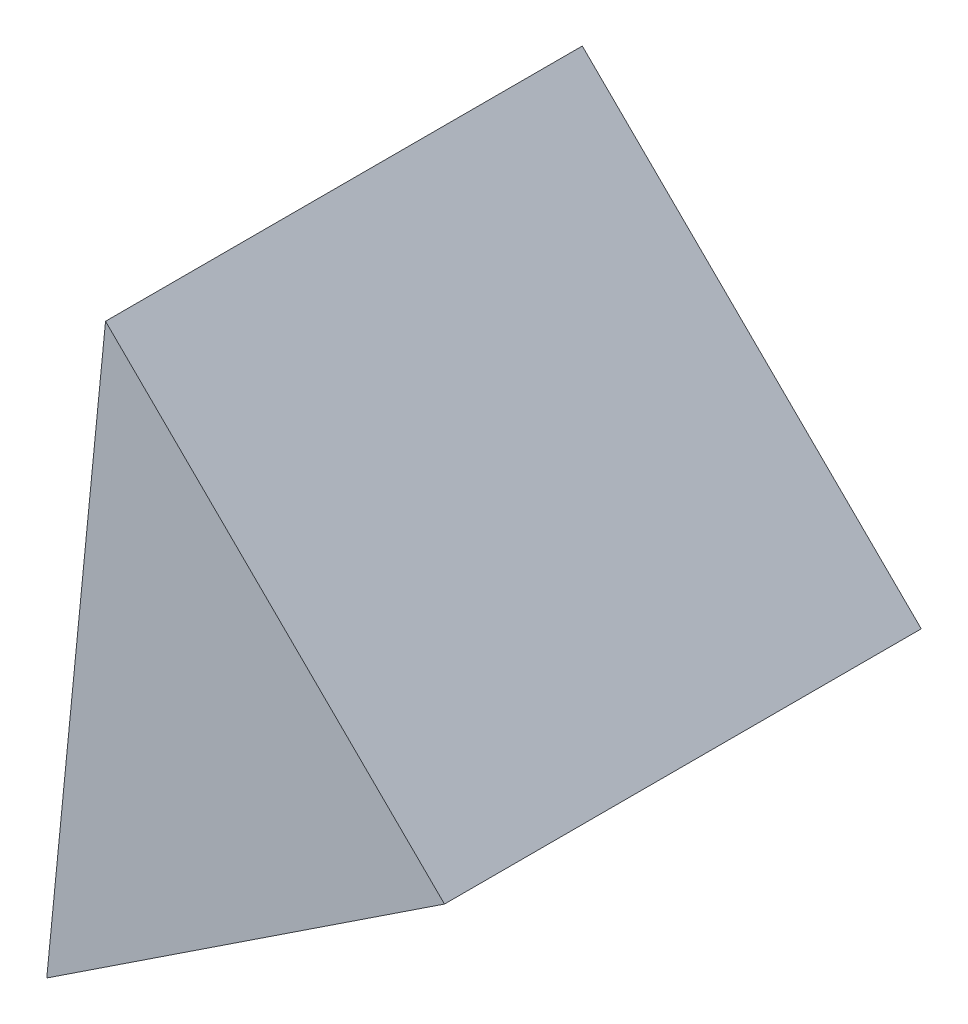
SolidWorks part; units mm, degrees
ref_plane "前视基准面" through (0, 0, 0) normal (0, 0, 1) x (1, 0, 0)
ref_plane "上视基准面" through (0, 0, 0) normal (0, 1, 0) x (1, 0, 0)
ref_plane "右视基准面" through (0, 0, 0) normal (1, 0, 0) x (0, 0, -1)
sketch "草图2" plane through (0, 0, 0) normal (0, 0, 1) x (1, 0, 0)
  line L0 (13.1998, 9.1185) -> (2.5352, 19.6668)
  line L1 (13.1998, 9.1185) -> (0.6862, 0.8475)
  line L2 (0.6862, 0.8475) -> (2.5352, 19.6668)
  dimension "D1" = 15
  dimension "D2" = 15
extrude "凸台-拉伸1" add sketch "草图2" along normal blind 15
